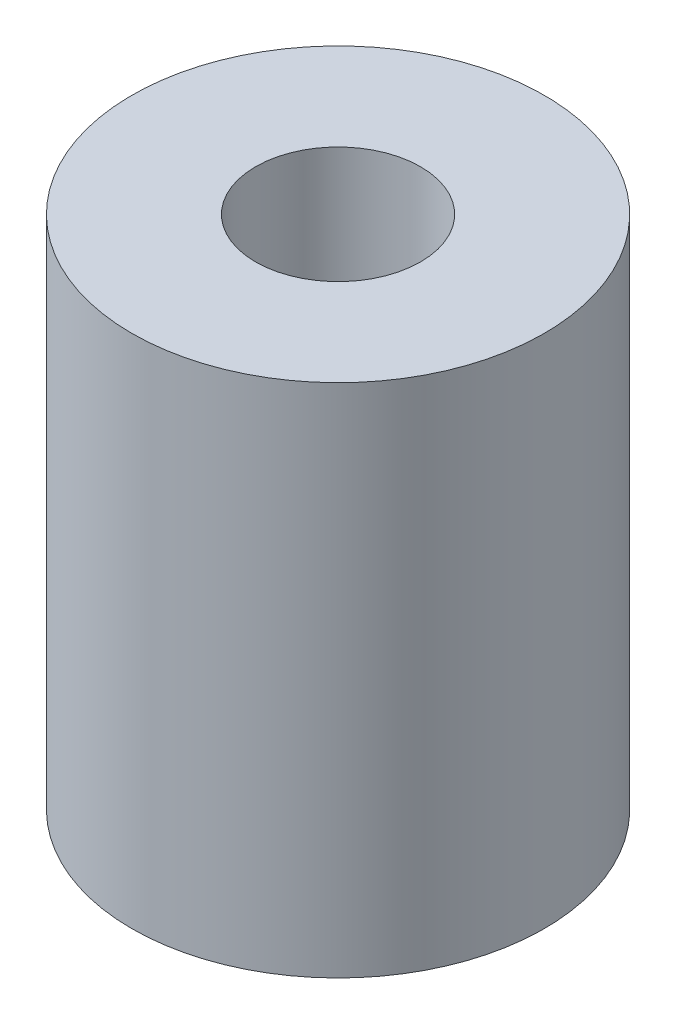
SolidWorks part; units mm, degrees
ref_plane "Front" through (0, 0, 0) normal (0, 0, 1) x (1, 0, 0)
ref_plane "Top" through (0, 0, 0) normal (0, 1, 0) x (1, 0, 0)
ref_plane "Right" through (0, 0, 0) normal (1, 0, 0) x (0, 0, -1)
sketch "Sketch1" plane through (0, 0, 0) normal (0, 1, 0) x (1, 0, 0)
  circle A0 centre (0, 0) radius 10
  circle A1 centre (0, 0) radius 2.5 construction
  dimension "D1" = 20
  dimension "D2" = 5
extrude "Boss-Extrude1" add sketch "Sketch1" along normal blind 25
sketch "Sketch2" plane through (0, 25, 0) normal (0, 1, 0) x (1, 0, 0)
  circle A0 centre (0, 0) radius 4
  dimension "D1" = 8
extrude "Cut-Extrude1" cut sketch "Sketch2" against normal blind 9
sketch "Sketch3" plane through (0, 0, 0) normal (0, -1, 0) x (-1, 0, 0)
  circle A0 centre (0, 0) radius 2.5
  dimension "D1" = 5
extrude "Cut-Extrude2" cut sketch "Sketch3" against normal blind 11
